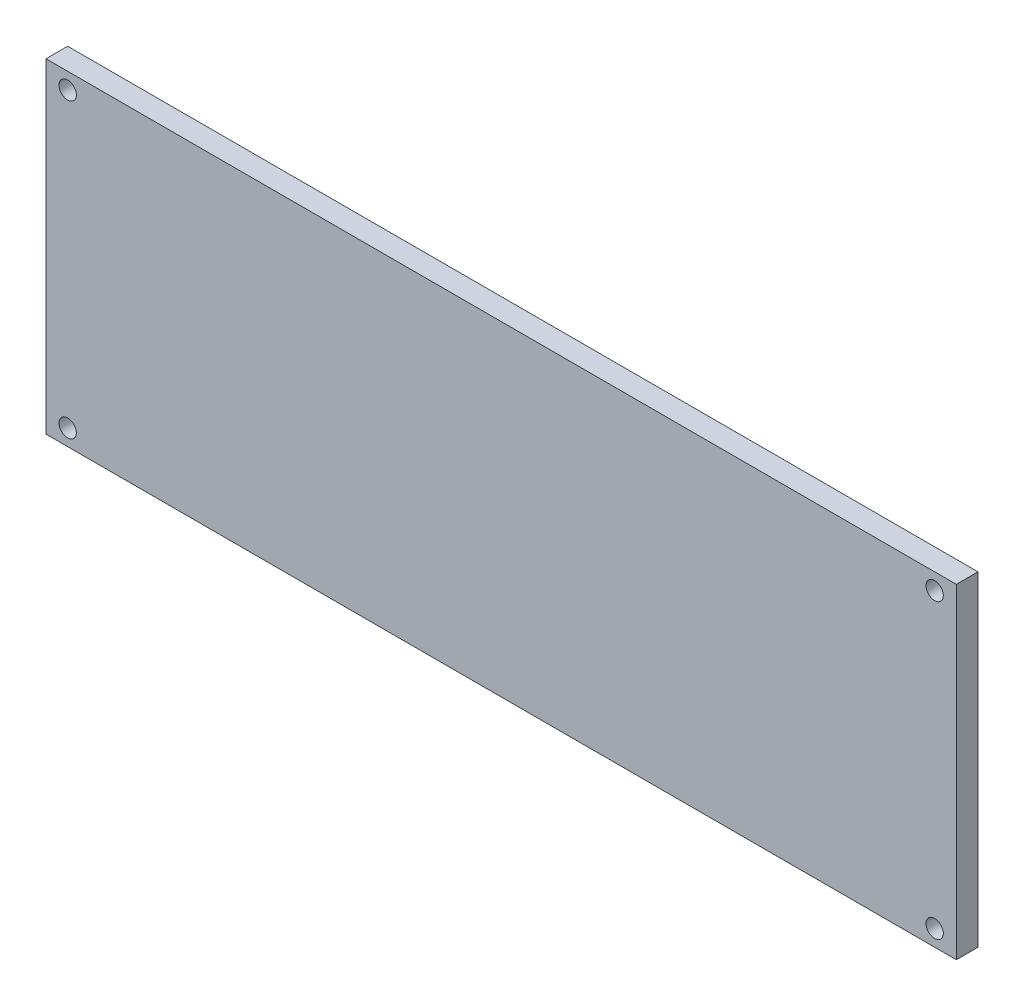
SolidWorks part; units mm, degrees
ref_plane "Front Plane" through (0, 0, 0) normal (0, 0, 1) x (1, 0, 0)
ref_plane "Top Plane" through (0, 0, 0) normal (0, 1, 0) x (1, 0, 0)
ref_plane "Right Plane" through (0, 0, 0) normal (1, 0, 0) x (0, 0, -1)
sketch "Sketch1" plane through (0, 0, 0) normal (0, 0, 1) x (1, 0, 0)
  line L1 (0, 0) -> (210, 0)
  line L2 (0, 0) -> (0, 75)
  line L3 (0, 75) -> (210, 75)
  line L4 (210, 0) -> (210, 75)
  dimension "D1" = 210
  dimension "D2" = 75
extrude "Boss-Extrude1" add sketch "Sketch1" along normal blind 5
sketch "Sketch2" plane through (0, 0, 0) normal (0, 0, -1) x (-1, 0, 0)
  line L0 (-210, 0) -> (-210, 75) construction
  line L1 (-210, 75) -> (0, 75) construction
  line L2 (-210, 37.5) -> (26.7735, 37.5) construction
  line L3 (-105, 75) -> (-105, -5.2129) construction
  circle A0 centre (-205, 71.25) radius 2
  circle A1 centre (-5, 71.25) radius 2
  circle A2 centre (-5, 3.75) radius 2
  circle A3 centre (-205, 3.75) radius 2
  dimension "D1" = 5
  dimension "D3" = 4
  dimension "D2" = 3.75
extrude "Cut-Extrude2" cut sketch "Sketch2" against normal blind 5 contours A3 | A2 | A1 | A0
